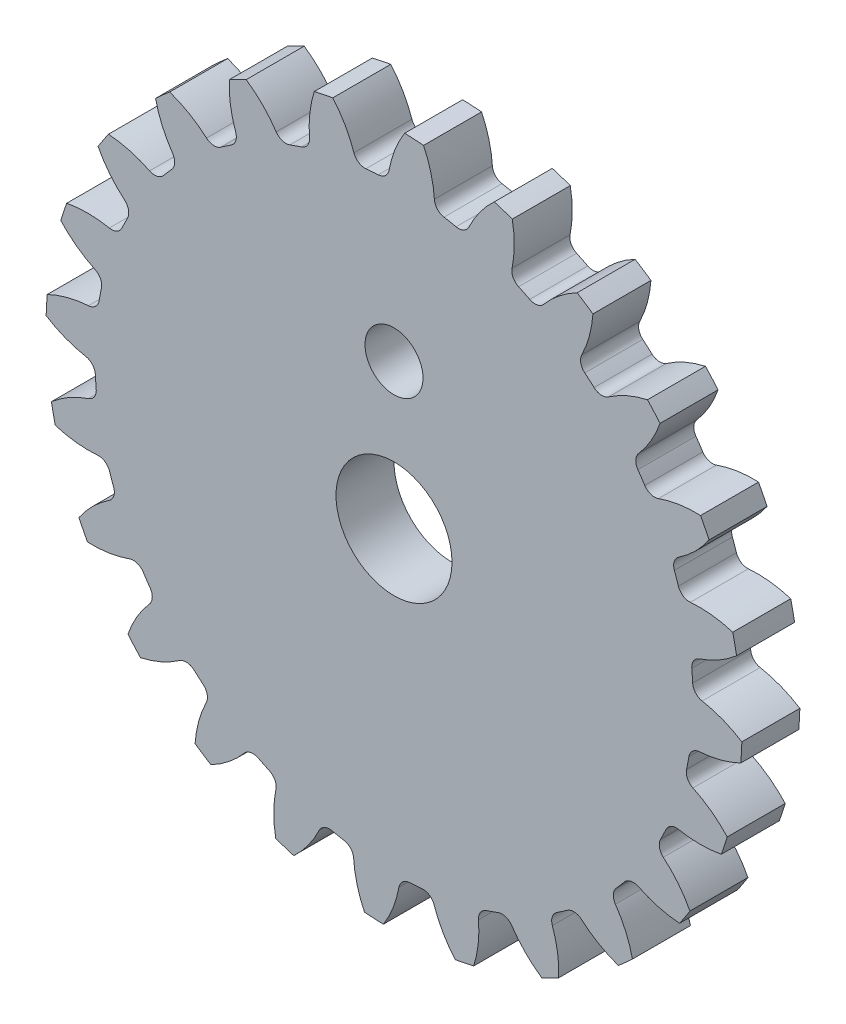
SolidWorks part; units mm, degrees
ref_plane "Alzado" through (0, 0, 0) normal (0, 0, 1) x (1, 0, 0)
ref_plane "Planta" through (0, 0, 0) normal (0, 1, 0) x (1, 0, 0)
ref_plane "Vista lateral" through (0, 0, 0) normal (1, 0, 0) x (0, 0, -1)
sketch "Croquis1" plane through (0, 0, 0) normal (0, 0, 1) x (1, 0, 0)
  circle A0 centre (0, 0) radius 30
  dimension "D1" = 60
extrude "Saliente-Extruir1" add sketch "Croquis1" along normal mid plane 5
sketch "Croquis2" plane through (0, 0, 2.5) normal (0, 0, 1) x (1, 0, 0)
  arc A0 (0.9153, 29.986) -> (-5.278, 29.5321) centre (0, 0) ccw
  arc A2 (-1.3543, 25.7472) -> (-2.4146, 25.6694) centre (0, 0) ccw
  arc A3 (0.9153, 29.986) -> (-0.4231, 26.5658) centre (9.0392, 24.835) ccw
  arc A4 (-5.278, 29.5321) -> (-3.4552, 26.3436) centre (-12.564, 23.2515) cw
  arc A5 (-0.4231, 26.5658) -> (-1.3543, 25.7472) centre (-1.4068, 26.7458) cw
  arc A6 (-3.4552, 26.3436) -> (-2.4146, 25.6694) centre (-2.5083, 26.665) ccw
  dimension "D1" = 51.5655
  dimension "D2" = 1
  dimension "D3" = 60
extrude "Cortar-Extruir1" cut sketch "Croquis2" against normal through all
pattern_circular "MatrizC1" count 24 every 15 about axis through (0, 0, 0) along (0, 0, 1) of "Cortar-Extruir1"
sketch "Croquis3" plane through (0, 0, 2.5) normal (0, 0, 1) x (1, 0, 0)
  circle A0 centre (0, 0) radius 5
  circle A1 centre (0, 0) radius 12.5 construction
  circle A2 centre (0, 12.5) radius 2.5
  dimension "D1" = 10
  dimension "D2" = 25
  dimension "D3" = 5
extrude "Cortar-Extruir2" cut sketch "Croquis3" against normal through all
